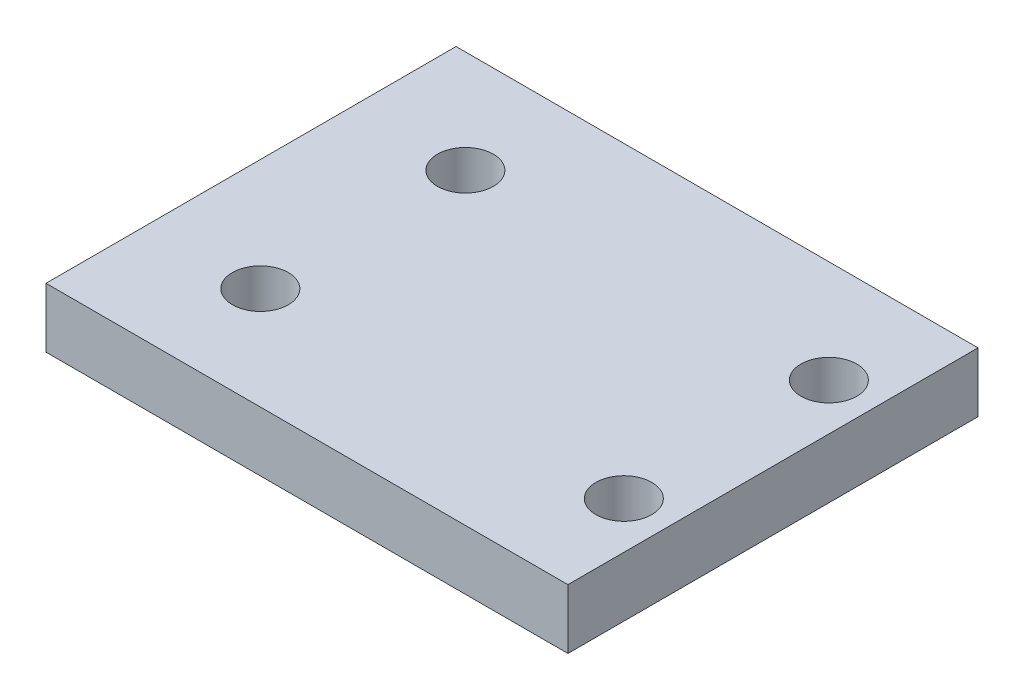
SolidWorks part; units mm, degrees
material "Custom Plastic"
ref_plane "Front Plane" through (0, 0, 0) normal (0, 0, 1) x (1, 0, 0)
ref_plane "Top Plane" through (0, 0, 0) normal (0, 1, 0) x (1, 0, 0)
ref_plane "Right Plane" through (0, 0, 0) normal (1, 0, 0) x (0, 0, -1)
sketch "Sketch1" plane through (0, 0, 0) normal (0, 1, 0) x (1, 0, 0)
  line L0 (-28, 44) -> (-28, 0)
  line L1 (-28, 0) -> (28, 0)
  line L2 (28, 0) -> (28, 44)
  line L3 (28, 44) -> (-28, 44)
  circle A0 centre (-16, 33) radius 3
  circle A1 centre (-16, 11) radius 3
  circle A2 centre (23, 33) radius 3
  circle A3 centre (23, 11) radius 3
  dimension "D1" = 6
  dimension "D2" = 6
  dimension "D3" = 6
  dimension "D4" = 6
  dimension "D5" = 12
  dimension "D8" = 11
  dimension "D12" = 11
  dimension "D14" = 11
  dimension "D6" = 56
  dimension "D7" = 44
  dimension "D9" = 12
  dimension "D10" = 5
  dimension "D11" = 5
  dimension "D13" = 22
extrude "Boss-Extrude1" add sketch "Sketch1" along normal blind 6.4
